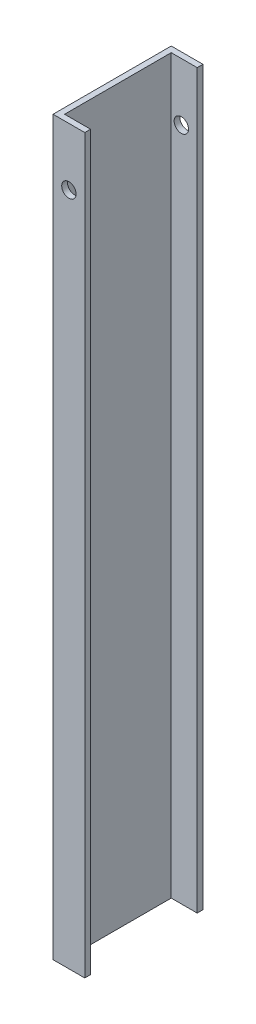
SolidWorks part; units mm, degrees
ref_plane "Front Plane" through (0, 0, 0) normal (0, 0, 1) x (1, 0, 0)
ref_plane "Top Plane" through (0, 0, 0) normal (0, 1, 0) x (1, 0, 0)
ref_plane "Right Plane" through (0, 0, 0) normal (1, 0, 0) x (0, 0, -1)
sketch "Sketch1" plane through (0, 0, 0) normal (0, 1, 0) x (1, 0, 0)
  line L0 (0, 0) -> (0, 41)
  line L1 (0, 41) -> (11, 41)
  line L2 (11, 41) -> (11, 39)
  line L3 (11, 39) -> (2, 39)
  line L4 (2, 39) -> (2, 2)
  line L5 (2, 2) -> (11, 2)
  line L6 (11, 2) -> (11, 0)
  line L7 (11, 0) -> (0, 0)
  line L8 (11, 2) -> (11, 39) construction
  line L9 (0, 20.5) -> (2, 20.5) construction
  dimension "D1" = 41
  dimension "D2" = 2
  dimension "D3" = 11
extrude "Boss-Extrude1" add sketch "Sketch1" along normal blind 254
sketch "Sketch2" plane through (0, 0, 0) normal (0, 0, 1) x (1, 0, 0)
  line L0 (5.5, 234) -> (5.5, 254) construction
  line L1 (0, 254) -> (11, 254) construction
  circle A0 centre (5.5, 234) radius 2.5
  dimension "D1" = 5
  dimension "D2" = 20
extrude "Cut-Extrude1" cut sketch "Sketch2" against normal through all
